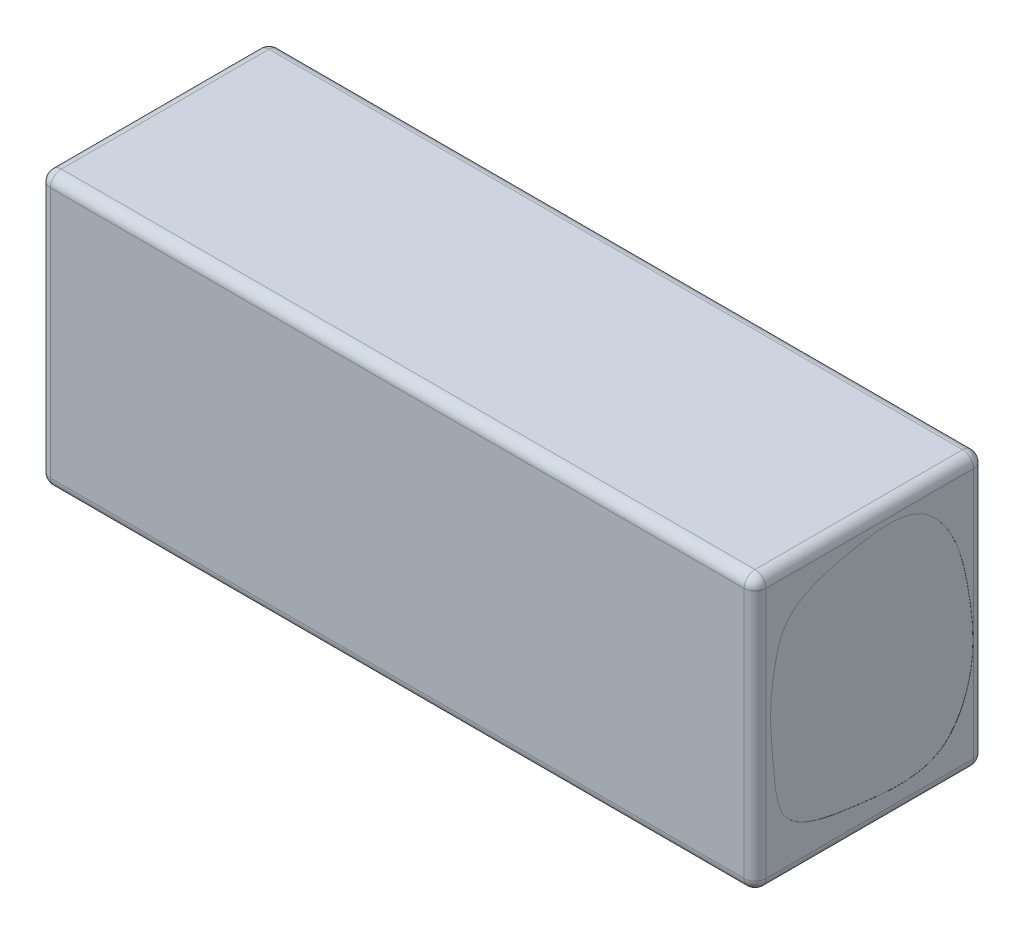
SolidWorks part; units mm, degrees
ref_plane "Alzado" through (0, 0, 0) normal (0, 0, 1) x (1, 0, 0)
ref_plane "Planta" through (0, 0, 0) normal (0, 1, 0) x (1, 0, 0)
ref_plane "Vista lateral" through (0, 0, 0) normal (1, 0, 0) x (0, 0, -1)
sketch "Croquis2" plane through (0, 0, 0) normal (0, 1, 0) x (1, 0, 0)
  line L1 (-65.5, 21) -> (65.5, 21)
  line L2 (-65.5, 21) -> (-65.5, -21)
  line L3 (-65.5, -21) -> (65.5, -21)
  line L4 (65.5, 21) -> (65.5, -21)
  line L5 (-65.5, 21) -> (65.5, -21) construction
  line L6 (-65.5, -21) -> (65.5, 21) construction
  point P0 (0, 0)
  dimension "D1" = 42
  dimension "D2" = 131
extrude "Saliente-Extruir1" add sketch "Croquis2" along normal blind 50
sketch "Croquis3" plane through (65.5, 0, 0) normal (1, 0, 0) x (0, 0, -1)
  line L0 (21, 50) -> (21, 0) construction
  line L1 (-21, 0) -> (21, 0) construction
  spline S0 degree 3 poles (-18.5189, 27.1957) (-17.6215, 34.6059) (-15.0571, 43.0889) (-3.8596, 46.3625) (8.6798, 48.1548) (16.162, 38.8582) (18.505, 27.9396) (19.7797, 16.1685) (13.2612, 3.8415) (3.0385, 4.6224) (-6.441, 5.8) (-16.667, 7.4767) (-17.5433, 18.803) (-18.5189, 27.1957) (-17.6215, 34.6059) (-15.0571, 43.0889) knots -0.200734 -0.138837 -0.065526 0 0.032914 0.13179 0.239123 0.300139 0.384993 0.497154 0.570211 0.671371 0.697844 0.799266 0.861163 0.934474 1 1.032914 1.13179 1.239123 only from (-17.1121, 36.0063) to (-17.1121, 36.0063)
  dimension "D1" = 2.9023
  dimension "D2" = 6.0648
  dimension "D3" = 7.9624
  dimension "D4" = 11.3358
  dimension "D5" = 21
  dimension "D6" = 24.4077
  dimension "D7" = 25.251
  dimension "D8" = 36.6363
  dimension "D9" = 38.1121
  dimension "D10" = 38.5338
  dimension "D11" = 39.1663
  dimension "D12" = 5.0132
  dimension "D13" = 5.4349
  dimension "D14" = 6.4891
  dimension "D15" = 10.2841
  dimension "D16" = 14.5009
  dimension "D17" = 18.0851
  dimension "D18" = 27.5728
  dimension "D19" = 29.0487
  dimension "D20" = 36.0063
  dimension "D21" = 39.5905
  dimension "D22" = 40.0122
  dimension "D23" = 45.494
  dimension "D24" = 45.9156
extrude "Cortar-Extruir1" cut sketch "Croquis3" against normal blind 0.02
fillet "Redondeo1" radius 2 12 edges at (-65.5, 25, -21) (-65.5, 0, 0) (0, 0, -21) (-65.5, 50, 0) (-65.5, 25, 21) (0, 0, 21) (65.5, 25, 21) (65.5, 0, 0) (65.5, 25, -21) (65.5, 50, 0) (0, 50, -21) (0, 50, 21)
sketch "Croquis4" plane through (-65.5, 0, 0) normal (-1, 0, 0) x (0, 0, 1)
  spline S0 degree 3 poles (15.2359, 38.5245) (7.5282, 44.5694) (-1.1498, 41.7397) (-9.762, 44.5548) (-16.5108, 37.6722) (-13.6393, 25.8617) (-23.1054, 3.3463) (-6.6507, 8.7556) (2.2855, 3.422) (9.7987, 8.1792) (16.6332, 13.2239) (14.8284, 19.8376) (15.3353, 26.1537) (13.3589, 31.415) (15.2359, 38.5245) (7.5282, 44.5694) (-1.1498, 41.7397) knots -0.160715 -0.108398 -0.052567 0 0.09132 0.159388 0.195314 0.3005 0.464636 0.542296 0.617263 0.70222 0.735858 0.814489 0.839285 0.891602 0.947433 1 1.09132 1.159388 1.195314 only from (8.9787, 42.5588) to (8.9787, 42.5588)
extrude "Cortar-Extruir2" cut sketch "Croquis4" against normal blind 2
sketch "Croquis5" plane through (0, 0, 0) normal (0, 0, 1) x (1, 0, 0)
  line L0 (-63.5, 60.336) -> (-63.5, -24.8178) construction
  line L1 (-65.5, 2) -> (-65.5, 48) construction
  spline S0 degree 3 poles (-53.8618, 32.7328) (-69.5509, 50.7867) (-80.9722, 33.3102) (-100.6899, 16.5259) (-122.6891, 9.3431) (-146.8961, -4.2029) (-174.4125, -0.4365) (-175.1989, 13.5819) knots 0 0 0 0 0.269002 0.38794 0.555143 0.749302 1 1 1 1
  dimension "D1" = 2
ref_plane "Plano2" through (0, 44.3516, 0) normal (0, 1, 0) x (1, 0, 0)
sketch "Croquis8" plane through (0, 44.3516, 0) normal (0, 1, 0) x (1, 0, 0)
  line L1 (-175.1989, 0) -> (-53.8618, 0) construction
  spline S0 degree 3 poles (-55.3555, 16.2982) (-63.3636, -14.8498) (-92.5607, 9.1001) (-132.2141, 7.0652) (-158.1556, -3.1561) (-176.8729, -7.2706) (-182.4957, 0) knots 0 0 0 0 0.383783 0.63197 0.829941 1 1 1 1
curve "Curva3"
ref_plane "Plano4" through (0, 13.5819, 0) normal (0, 1, 0) x (1, 0, 0)
sketch "Croquis16" plane through (0, 0, 0) normal (0, 0, 1) x (1, 0, 0)
  spline S0 degree 3 poles (-53.9384, 4.992) (-66.6358, 10.7057) (-81.9431, 2.3946) (-101.9354, 0.6145) (-118.1272, 9.4733) (-115.9531, 30.412) (-133.7299, 22.2132) knots 0 0 0 0 0.399614 0.578444 0.629928 1 1 1 1
sketch "Croquis17" plane through (0, 0, 0) normal (0, 1, 0) x (1, 0, 0)
  spline S0 degree 3 poles (-52.1285, 14.4463) (-66.7421, 3.0669) (-76.004, 19.5837) (-95.7769, 26.6431) (-116.1211, 29.0115) (-124.7369, 10.6242) (-135.886, 23.7) knots 0 0 0 0 0.385919 0.507884 0.705731 1 1 1 1
curve "Curva4"
ref_plane "Plano5" through (-133.7299, 0, 0) normal (1, 0, 0) x (0, 0, -1)
